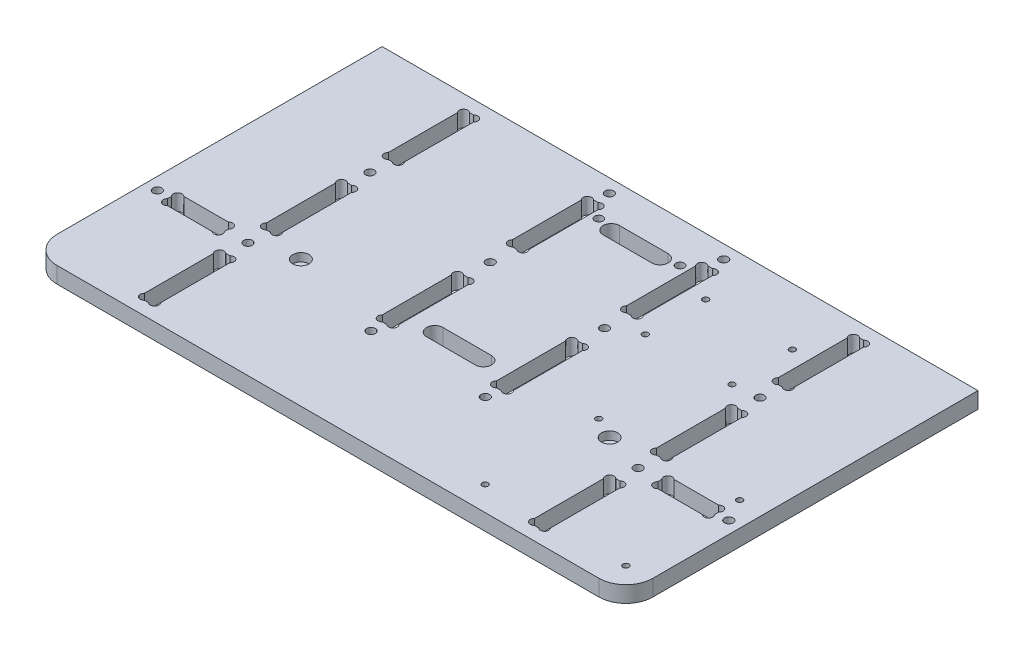
SolidWorks part; units mm, degrees
ref_plane "Plan de face" through (0, 0, 0) normal (0, 0, 1) x (1, 0, 0)
ref_plane "Plan de dessus" through (0, 0, 0) normal (0, 1, 0) x (1, 0, 0)
ref_plane "Plan de droite" through (0, 0, 0) normal (1, 0, 0) x (0, 0, -1)
sketch "Esquisse2" plane through (0, 0, 0) normal (0, 1, 0) x (1, 0, 0)
  line L0 (-40.8344, 65) -> (14.2855, 65) construction
  line L1 (0, 0) -> (160, 0) construction
  line L2 (0, 0) -> (0, 130) construction
  line L3 (0, 130) -> (160, 130) construction
  line L4 (160, 0) -> (160, 130) construction
  line L5 (80, 138.5727) -> (80, -10.0112) construction
  line L6 (5, 135.8712) -> (5, -2.4469) construction
  line L7 (11, 135.8712) -> (11, -2.4469) construction
  line L8 (-6.6063, 125) -> (16.2666, 125) construction
  line L9 (-6.6063, 95) -> (14.2855, 95) construction
  line L10 (2.2186, 87.5) -> (10.8635, 87.5) construction
  line L11 (-5.1655, 80) -> (14.2855, 80) construction
  line L12 (8, 98.5901) -> (8, 83.9707) construction
  line L13 (2.2186, 110) -> (14.2855, 110) construction
  line L14 (5, 125) -> (21.8611, 108.1389) construction
  line L15 (7.2627, 125) -> (8.7373, 125)
  line L16 (11, 122.7373) -> (11, 97.2627)
  line L17 (8.7373, 95) -> (7.2627, 95)
  line L18 (5, 97.2627) -> (5, 122.7373)
  line L19 (7.2627, 80) -> (8.7373, 80)
  line L20 (7.2627, 50) -> (8.7373, 50)
  line L21 (8.7373, 35) -> (7.2627, 35)
  line L22 (5, 32.7373) -> (5, 7.2627)
  line L23 (11, 7.2627) -> (11, 32.7373)
  line L24 (7.2627, 5) -> (8.7373, 5)
  line L25 (5, 77.7373) -> (5, 52.2627)
  line L26 (11, 52.2627) -> (11, 77.7373)
  line L27 (152.7373, 5) -> (151.2627, 5)
  line L28 (155, 32.7373) -> (155, 7.2627)
  line L29 (149, 7.2627) -> (149, 32.7373)
  line L30 (151.2627, 35) -> (152.7373, 35)
  line L31 (155, 77.7373) -> (155, 52.2627)
  line L32 (149, 52.2627) -> (149, 77.7373)
  line L33 (152.7373, 50) -> (151.2627, 50)
  line L34 (152.7373, 80) -> (151.2627, 80)
  line L35 (151.2627, 95) -> (152.7373, 95)
  line L36 (155, 97.2627) -> (155, 122.7373)
  line L37 (149, 122.7373) -> (149, 97.2627)
  line L38 (152.7373, 125) -> (151.2627, 125)
  line L39 (-30, 10) -> (-30, 130)
  line L40 (-30, 130) -> (190, 130)
  line L41 (190, -22.3136) -> (190, 138.5727) construction
  line L42 (-21, 53.7406) -> (-21, 30.6623) construction
  line L43 (23, 80.9657) -> (23, 16.2308) construction
  line L44 (14.2855, 5) -> (212.1831, 5) construction
  line L45 (58.9, 26.2966) -> (58.9, 131.6333) construction
  line L46 (167.2289, 47) -> (-33.5392, 47) construction
  line L47 (194.5567, 42.5) -> (-40.0739, 42.5) construction
  line L48 (-61.9181, 0) -> (207.7659, 0) construction
  line L49 (-30, -22.3136) -> (-30, 138.5727) construction
  line L50 (190, 130) -> (190, 10)
  line L51 (110.6, 138.5727) -> (110.6, -2.4469) construction
  line L52 (-31.7937, 39.5) -> (7.2627, 39.5) construction
  line L53 (-31.7937, 45.5) -> (3.2216, 45.5) construction
  line L54 (-21, 45.5) -> (-9.6603, 34.1603) construction
  line L55 (-10.5, 36.8014) -> (-10.5, 48.3974) construction
  line L56 (-25.5, 44.0604) -> (-25.5, 36.0648) construction
  line L57 (142.6, 138.5727) -> (142.6, -2.4469) construction
  line L58 (181, 41.7627) -> (181, 43.2373)
  line L59 (-2.2627, 39.5) -> (-18.7373, 39.5)
  line L60 (0, 41.7627) -> (0, 43.2373)
  line L61 (-2.2627, 45.5) -> (-18.7373, 45.5)
  line L62 (98.0388, 108.86) -> (201.9173, 108.86) construction
  line L63 (-21, 41.7627) -> (-21, 43.2373)
  line L64 (162.2627, 39.5) -> (178.7373, 39.5)
  line L65 (162.2627, 45.5) -> (178.7373, 45.5)
  line L66 (160, 41.7627) -> (160, 43.2373)
  line L67 (-20, 0) -> (180, 0)
  line L68 (71, 51.4) -> (89, 51.4)
  line L69 (71, 62.6311) -> (71, 30.6623) construction
  line L70 (160, 143.685) -> (160, 132.6292) construction
  line L71 (89, 45.4) -> (71, 45.4)
  line L72 (95.9898, 45.4) -> (66.0104, 45.4) construction
  line L73 (89, 116.6) -> (71, 116.6)
  line L74 (66.0104, 51.4) -> (95.9898, 51.4) construction
  line L75 (48.7628, 81) -> (100.0085, 81) construction
  line L76 (71, 110.6) -> (89, 110.6)
  line L77 (104.2, 140.4327) -> (104.2, 122.7373) construction
  line L78 (-42.5393, 130) -> (225.0832, 130) construction
  line L79 (48.7628, 120) -> (64.7136, 120) construction
  line L80 (62, 138.5727) -> (62, 32.7373) construction
  line L81 (48.7628, 90) -> (66.0104, 90) construction
  line L82 (55.8, 138.5727) -> (55.8, 32.7374) construction
  line L83 (53.8535, 125) -> (70, 125) construction
  line L84 (66.0104, 105) -> (48.7628, 105) construction
  line L85 (55.8, 90) -> (69.6573, 103.8573) construction
  line L86 (62, 44.2627) -> (62, 69.7373)
  line L87 (58.0627, 120) -> (59.7373, 120)
  line L88 (55.8, 117.7373) -> (55.8, 92.2627)
  line L89 (58.0627, 90) -> (59.7373, 90)
  line L90 (62, 117.7373) -> (62, 92.2627)
  line L91 (55.8, 44.2627) -> (55.8, 69.7373)
  line L92 (58.0627, 72) -> (59.7373, 72)
  line L93 (58.0627, 42) -> (59.7373, 42)
  line L94 (101.9373, 42) -> (100.2627, 42)
  line L95 (98, 44.2627) -> (98, 69.7373)
  line L96 (104.2, 44.2627) -> (104.2, 69.7373)
  line L97 (101.9373, 72) -> (100.2627, 72)
  line L98 (101.9373, 90) -> (100.2627, 90)
  line L99 (104.2, 117.7373) -> (104.2, 92.2627)
  line L100 (98, 117.7373) -> (98, 92.2627)
  line L101 (101.9373, 120) -> (100.2627, 120)
  line L102 (63.8206, 48.4) -> (72.4785, 48.4) construction
  line L103 (126.6, 140.4327) -> (126.6, 122.7373) construction
  line L104 (107.8332, 86.56) -> (201.9173, 86.56) construction
  line L105 (104.2, 81) -> (225.0832, 81) construction
  line L106 (107.8332, 120.5) -> (218.665, 120.5) construction
  line L107 (115.1445, 55) -> (212.1831, 55) construction
  line L108 (125, -14.9305) -> (125, 58.8548) construction
  line L109 (185, -14.9305) -> (185, 62.6311) construction
  line L110 (181, 30) -> (198.5899, 30) construction
  line L111 (155, 8.6337) -> (155, -6.7089) construction
  line L112 (176.1, 9) -> (188.1073, 9) construction
  line L113 (181, 2.5348) -> (181, 17.6869) construction
  arc A0 (7.2627, 125) -> (5, 122.7373) centre (6.1314, 123.8686) ccw
  arc A1 (8.7373, 125) -> (11, 122.7373) centre (9.8686, 123.8686) cw
  arc A2 (7.2627, 95) -> (5, 97.2627) centre (6.1314, 96.1314) cw
  arc A3 (8.7373, 95) -> (11, 97.2627) centre (9.8686, 96.1314) ccw
  arc A4 (7.2627, 80) -> (5, 77.7373) centre (6.1314, 78.8686) ccw
  arc A5 (8.7373, 80) -> (11, 77.7373) centre (9.8686, 78.8686) cw
  arc A6 (7.2627, 50) -> (5, 52.2627) centre (6.1314, 51.1314) cw
  arc A7 (8.7373, 50) -> (11, 52.2627) centre (9.8686, 51.1314) ccw
  arc A8 (8.7373, 35) -> (11, 32.7373) centre (9.8686, 33.8686) cw
  arc A9 (7.2627, 35) -> (5, 32.7373) centre (6.1314, 33.8686) ccw
  arc A10 (8.7373, 5) -> (11, 7.2627) centre (9.8686, 6.1314) ccw
  arc A11 (7.2627, 5) -> (5, 7.2627) centre (6.1314, 6.1314) cw
  arc A12 (151.2627, 5) -> (149, 7.2627) centre (150.1314, 6.1314) cw
  arc A13 (152.7373, 5) -> (155, 7.2627) centre (153.8686, 6.1314) ccw
  arc A14 (151.2627, 35) -> (149, 32.7373) centre (150.1314, 33.8686) ccw
  arc A15 (152.7373, 35) -> (155, 32.7373) centre (153.8686, 33.8686) cw
  arc A16 (151.2627, 50) -> (149, 52.2627) centre (150.1314, 51.1314) cw
  arc A17 (152.7373, 50) -> (155, 52.2627) centre (153.8686, 51.1314) ccw
  arc A18 (152.7373, 80) -> (155, 77.7373) centre (153.8686, 78.8686) cw
  arc A19 (151.2627, 80) -> (149, 77.7373) centre (150.1314, 78.8686) ccw
  arc A20 (151.2627, 95) -> (149, 97.2627) centre (150.1314, 96.1314) cw
  arc A21 (152.7373, 95) -> (155, 97.2627) centre (153.8686, 96.1314) ccw
  arc A22 (151.2627, 125) -> (149, 122.7373) centre (150.1314, 123.8686) ccw
  arc A23 (152.7373, 125) -> (155, 122.7373) centre (153.8686, 123.8686) cw
  circle A24 centre (8, 87.5) radius 1.6
  circle A25 centre (8, 42.5) radius 1.6
  circle A26 centre (152, 42.5) radius 1.6
  circle A27 centre (152, 87.5) radius 1.6
  circle A28 centre (58.9, 125) radius 1.6
  circle A29 centre (110.6, 108.86) radius 1.1
  arc A30 (71, 51.4) -> (71, 45.4) centre (71, 48.4) ccw
  arc A31 (-18.7373, 45.5) -> (-21, 43.2373) centre (-19.8686, 44.3686) ccw
  circle A32 centre (-25.5, 42.5) radius 1.6
  arc A33 (-18.7373, 39.5) -> (-21, 41.7627) centre (-19.8686, 40.6314) cw
  arc A34 (-2.2627, 45.5) -> (0, 43.2373) centre (-1.1314, 44.3686) cw
  arc A35 (-2.2627, 39.5) -> (0, 41.7627) centre (-1.1314, 40.6314) ccw
  circle A36 centre (185.5, 42.5) radius 1.6
  arc A37 (178.7373, 45.5) -> (181, 43.2373) centre (179.8686, 44.3686) cw
  arc A38 (178.7373, 39.5) -> (181, 41.7627) centre (179.8686, 40.6314) ccw
  arc A39 (162.2627, 45.5) -> (160, 43.2373) centre (161.1314, 44.3686) ccw
  arc A40 (162.2627, 39.5) -> (160, 41.7627) centre (161.1314, 40.6314) cw
  circle A41 centre (110.6, 86.56) radius 1.1
  circle A42 centre (58.9, 81) radius 1.6
  arc A43 (89, 51.4) -> (89, 45.4) centre (89, 48.4) cw
  arc A44 (-30, 10) -> (-20, 0) centre (-20, 10) ccw
  arc A45 (190, 10) -> (180, 0) centre (180, 10) cw
  arc A46 (71, 110.6) -> (71, 116.6) centre (71, 113.6) cw
  arc A47 (89, 110.6) -> (89, 116.6) centre (89, 113.6) ccw
  arc A48 (55.8, 92.2627) -> (58.0627, 90) centre (56.9314, 91.1314) ccw
  arc A49 (62, 92.2627) -> (59.7373, 90) centre (60.8686, 91.1314) cw
  arc A50 (55.8, 117.7373) -> (58.0627, 120) centre (56.9314, 118.8686) cw
  arc A51 (62, 117.7373) -> (59.7373, 120) centre (60.8686, 118.8686) ccw
  arc A52 (55.8, 69.7373) -> (58.0627, 72) centre (56.9314, 70.8686) cw
  arc A53 (62, 69.7373) -> (59.7373, 72) centre (60.8686, 70.8686) ccw
  arc A54 (55.8, 44.2627) -> (58.0627, 42) centre (56.9314, 43.1314) ccw
  arc A55 (62, 44.2627) -> (59.7373, 42) centre (60.8686, 43.1314) cw
  circle A56 centre (58.9, 37) radius 1.6
  circle A57 centre (101.1, 37) radius 1.6
  arc A58 (104.2, 44.2627) -> (101.9373, 42) centre (103.0686, 43.1314) cw
  arc A59 (98, 44.2627) -> (100.2627, 42) centre (99.1314, 43.1314) ccw
  arc A60 (104.2, 69.7373) -> (101.9373, 72) centre (103.0686, 70.8686) ccw
  arc A61 (98, 69.7373) -> (100.2627, 72) centre (99.1314, 70.8686) cw
  circle A62 centre (101.1, 81) radius 1.6
  arc A63 (98, 92.2627) -> (100.2627, 90) centre (99.1314, 91.1314) ccw
  arc A64 (104.2, 92.2627) -> (101.9373, 90) centre (103.0686, 91.1314) cw
  arc A65 (104.2, 117.7373) -> (101.9373, 120) centre (103.0686, 118.8686) ccw
  arc A66 (98, 117.7373) -> (100.2627, 120) centre (99.1314, 118.8686) cw
  circle A67 centre (101.1, 125) radius 1.6
  circle A68 centre (142.6, 108.86) radius 1.1
  circle A69 centre (142.6, 86.56) radius 1.1
  circle A70 centre (181, 9) radius 1.1
  circle A71 centre (129, 9) radius 1.1
  circle A72 centre (129, 51) radius 1.1
  circle A73 centre (181, 51) radius 1.1
  point P187 (-30, 0)
  point P190 (190, 0)
  dimension "D10" = 12
  dimension "D11" = 3
  dimension "D17" = 18
  dimension "D19" = 10
  dimension "D18" = 9
  dimension "D22" = 34
  dimension "D26" = 16
  dimension "D28" = 15
  dimension "D30" = 22.4
  dimension "D32" = 45
  dimension "D34" = 16
  dimension "D24" = 39.5
  dimension "D33" = 3
  dimension "D1" = 5
  dimension "D2" = 5
  dimension "D3" = 6
  dimension "D4" = 3
  dimension "D5" = 30
  dimension "D6" = 15
  dimension "D7" = 45
  dimension "D8" = 15
  dimension "D9" = 7.5
  dimension "D12" = 6
  dimension "D13" = 21
  dimension "D14" = 10.5
  dimension "D15" = 45
  dimension "D16" = 4.5
  dimension "D20" = 1.6
  dimension "D21" = 6
  dimension "D23" = 3.1
  dimension "D25" = 6.2
  dimension "D27" = 9
  dimension "D29" = 30
  dimension "D31" = 5
  dimension "D35" = 11.64
  dimension "D36" = 49
  dimension "D37" = 22.3
  dimension "D38" = 50
  dimension "D39" = 5
  dimension "D40" = 60
  dimension "D41" = 30
  dimension "D42" = 25
  dimension "D43" = 4
  dimension "D44" = 4
extrude "Extrusion1" add sketch "Esquisse2" along normal blind 6
sketch "Esquisse4" plane through (0, 6, 0) normal (0, 1, 0) x (-1, 0, 0)
  line L0 (-80, -138.2004) -> (-80, 10.3402) construction
  line L1 (-14.6457, -47) -> (-146.6025, -47) construction
  line L2 (-51.7363, -115) -> (-126.4524, -115) construction
  line L3 (-65, -121.6166) -> (-65, -105.5678) construction
  line L4 (-23, -57.4214) -> (-23, -40.1244) construction
  circle A0 centre (-65, -115) radius 1.53
  circle A1 centre (-23, -47) radius 3
  circle A2 centre (-95, -115) radius 1.53
  circle A3 centre (-137, -47) radius 3
  dimension "D1" = 15
extrude "Enlèv. mat.-Extru.2" cut sketch "Esquisse4" against normal blind 3
